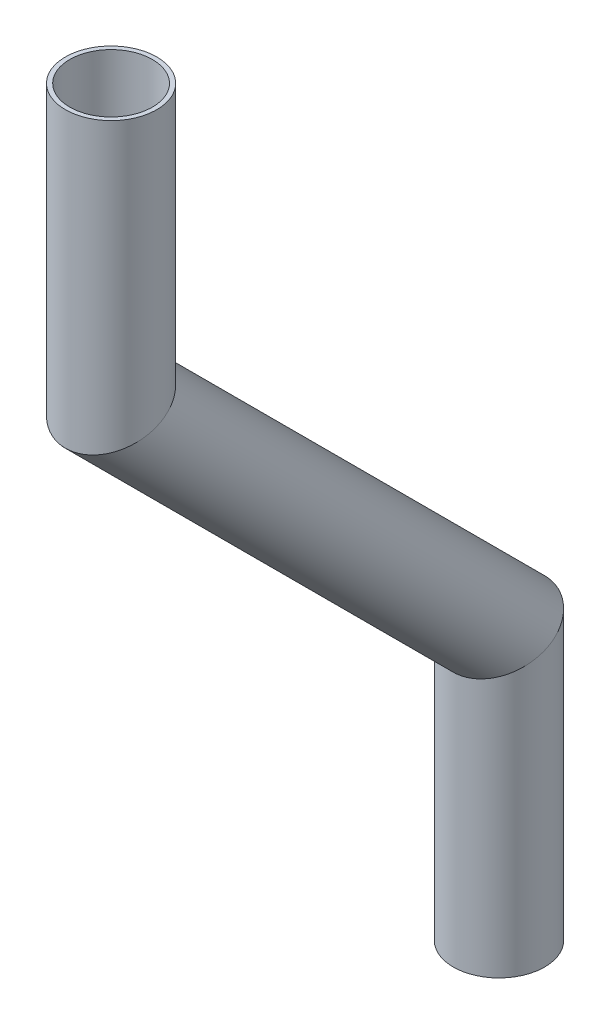
SolidWorks part; units mm, degrees
ref_plane "Front Plane" through (0, 0, 0) normal (0, 0, 1) x (1, 0, 0)
ref_plane "Top Plane" through (0, 0, 0) normal (0, 1, 0) x (1, 0, 0)
ref_plane "Right Plane" through (0, 0, 0) normal (1, 0, 0) x (0, 0, -1)
sketch "Sketch1" plane through (0, 0, 0) normal (1, 0, 0) x (0, 0, -1)
  line L0 (-302.5722, -54.9174) -> (-302.5722, -93.0174)
  line L1 (-302.5722, -93.0174) -> (-248.6906, -146.899)
  line L2 (-248.6906, -146.899) -> (-248.6906, -184.999)
  line L3 (-302.5722, -93.0174) -> (-302.5722, -130.7988) construction
  dimension "D1" = 45
  dimension "D2" = 38.1
  dimension "D3" = 38.1
  dimension "D4" = 76.2
other "Pipe 0.5 SCH 40(1)"
ref_plane "Plane1" through (0, -54.9174, 302.5722) normal (0, -1, 0) x (0, 0, -1)
sketch "Sketch11" plane through (0, -54.9174, 302.5722) normal (0, -1, 0) x (0, 0, -1)
  circle A0 centre (0, 0) radius 5.7404
  circle A1 centre (0, 0) radius 6.35
  point P5 (0, 0)
  dimension "In_dia" = 11.4808
  dimension "Out_dia" = 12.7
